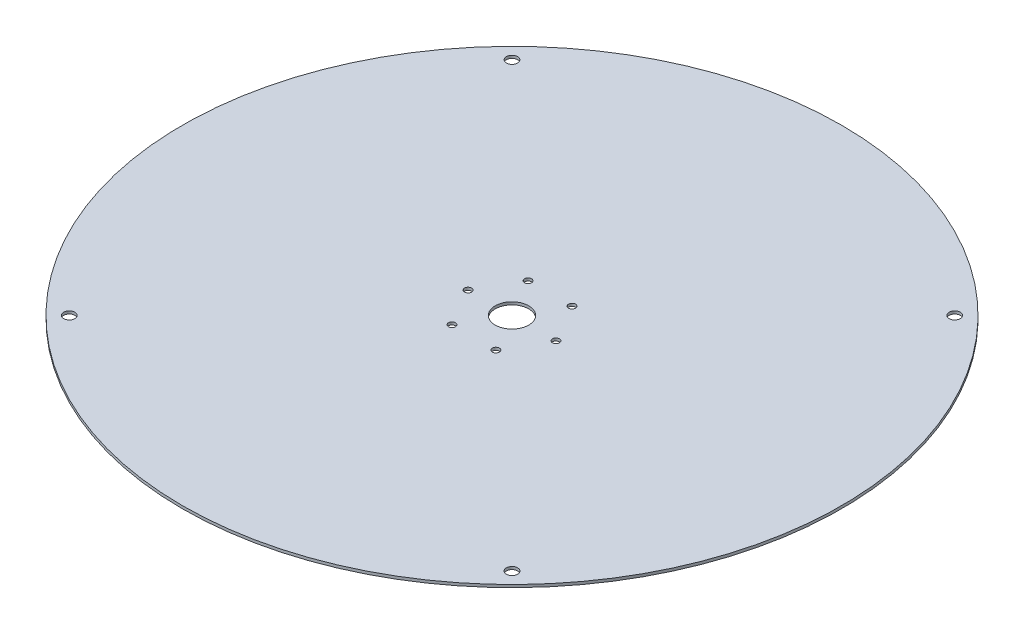
SolidWorks part; units mm, degrees
material "AISI 1020"
ref_plane "Alzado" through (0, 0, 0) normal (0, 0, 1) x (1, 0, 0)
ref_plane "Planta" through (0, 0, 0) normal (0, 1, 0) x (1, 0, 0)
ref_plane "Vista lateral" through (0, 0, 0) normal (1, 0, 0) x (0, 0, -1)
sketch "Croquis1" plane through (0, 0, 0) normal (0, 1, 0) x (1, 0, 0)
  circle A0 centre (0, 0) radius 375
  dimension "D1" = 750
extrude "Saliente-Extruir1" add sketch "Croquis1" along normal blind 3.1
sketch "Croquis3" plane through (0, 3.1, 0) normal (0, 1, 0) x (1, 0, 0)
  circle A0 centre (-251.8714, -251.8714) radius 6.35
  circle A1 centre (-251.8714, 251.8714) radius 6.35
  circle A2 centre (251.8714, 251.8714) radius 6.35
  circle A3 centre (251.8714, -251.8714) radius 6.35
  circle A4 centre (0, 0) radius 19.05
  point P0 (0, -356.2)
  point P1 (-251.8714, -251.8714)
  point P5 (-356.2, 0)
  point P6 (-251.8714, 251.8714)
  point P7 (0, 356.2)
  point P8 (251.8714, 251.8714)
  point P9 (356.2, 0)
  point P10 (251.8714, -251.8714)
  point P11 (0, 0)
  point P21 (0, 0)
  dimension "D3" = 12.7
  dimension "D5" = 38.1
  dimension "D6" = 356.2
  dimension "D1" = 356.2
  dimension "D2" = 8
  dimension "D4" = 4
extrude "Cortar-Extruir2" cut sketch "Croquis3" against normal through all
sketch "Croquis4" plane through (0, 3.1, 0) normal (0, 1, 0) x (1, 0, 0)
  circle A0 centre (50, 0) radius 4
  circle A1 centre (25, -43.3013) radius 4
  circle A2 centre (-25, -43.3013) radius 4
  circle A3 centre (-50, 0) radius 4
  circle A4 centre (-25, 43.3013) radius 4
  circle A5 centre (25, 43.3013) radius 4
  point P16 (0, 0)
  dimension "D1" = 8
  dimension "D2" = 50
  dimension "D3" = 6
extrude "Cortar-Extruir3" cut sketch "Croquis4" against normal through all
